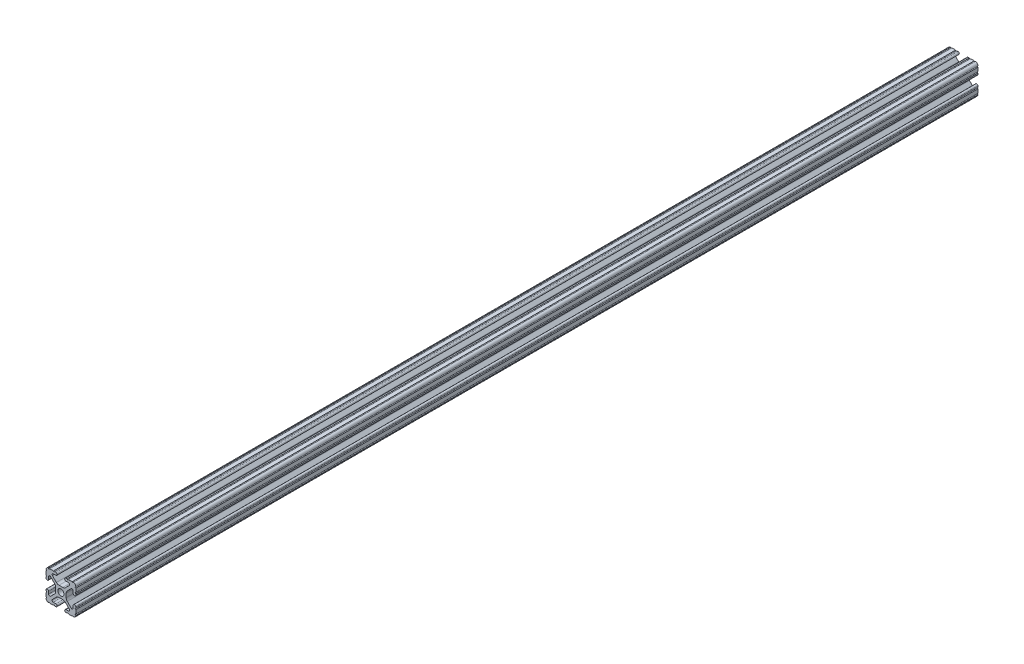
SolidWorks part; units mm, degrees
material "6061-T6 (SS)"
ref_plane "Front Plane" through (0, 0, 0) normal (0, 0, 1) x (1, 0, 0)
ref_plane "Top Plane" through (0, 0, 0) normal (0, 1, 0) x (1, 0, 0)
ref_plane "Right Plane" through (0, 0, 0) normal (1, 0, 0) x (0, 0, -1)
ref_plane "Plane1" through (0, 0, -450.85) normal (0, 0, -1) x (-1, 0, 0)
sketch "Sketch1" plane through (0, 0, -450.85) normal (0, 0, -1) x (-1, 0, 0)
  line L0 (12.7, -9.5504) -> (12.7, -6.3331)
  line L1 (12.7, -5.3171) -> (12.7, -4.3434)
  line L2 (10.4902, -4.3434) -> (10.4902, -6.4748)
  line L3 (8.7558, -7.1932) -> (5.4257, -3.8632)
  line L4 (4.4958, -1.6181) -> (4.4958, 1.6181)
  line L5 (5.4257, 3.8632) -> (8.7558, 7.1932)
  line L6 (10.4902, 6.4748) -> (10.4902, 4.3434)
  line L7 (12.7, 4.3434) -> (12.7, 5.3171)
  line L8 (12.7, 6.3331) -> (12.7, 9.5504)
  line L9 (9.5504, 12.7) -> (6.3331, 12.7)
  line L10 (5.3171, 12.7) -> (4.3434, 12.7)
  line L11 (4.3434, 10.4902) -> (6.4748, 10.4902)
  line L12 (7.1932, 8.7558) -> (3.8632, 5.4257)
  line L13 (1.6181, 4.4958) -> (-1.6181, 4.4958)
  line L14 (-3.8632, 5.4257) -> (-7.1932, 8.7558)
  line L15 (-6.4748, 10.4902) -> (-4.3434, 10.4902)
  line L16 (-4.3434, 12.7) -> (-5.3171, 12.7)
  line L17 (-6.3331, 12.7) -> (-9.5504, 12.7)
  line L18 (-12.7, 9.5504) -> (-12.7, 6.3331)
  line L19 (-12.7, 5.3171) -> (-12.7, 4.3434)
  line L20 (-10.4902, 4.3434) -> (-10.4902, 6.4748)
  line L21 (-8.7558, 7.1932) -> (-5.4257, 3.8632)
  line L22 (-4.4958, 1.6181) -> (-4.4958, -1.6181)
  line L23 (-5.4257, -3.8632) -> (-8.7558, -7.1932)
  line L24 (-10.4902, -6.4748) -> (-10.4902, -4.3434)
  line L25 (-12.7, -4.3434) -> (-12.7, -5.3171)
  line L26 (-12.7, -6.3331) -> (-12.7, -9.5504)
  line L27 (-9.5504, -12.7) -> (-6.3331, -12.7)
  line L28 (-5.3171, -12.7) -> (-4.3434, -12.7)
  line L29 (-4.3434, -10.4902) -> (-6.4748, -10.4902)
  line L30 (-7.1932, -8.7558) -> (-3.8632, -5.4257)
  line L31 (-1.6181, -4.4958) -> (1.6181, -4.4958)
  line L32 (3.8632, -5.4257) -> (7.1932, -8.7558)
  line L33 (6.4748, -10.4902) -> (4.3434, -10.4902)
  line L34 (4.3434, -12.7) -> (5.3171, -12.7)
  line L35 (6.3331, -12.7) -> (9.5504, -12.7)
  arc A0 (12.6998, -10.5664) -> (12.7, -9.5504) centre (12.7, -10.0584) cw
  arc A1 (12.7, -6.3331) -> (12.7, -5.3171) centre (12.7, -5.8251) cw
  arc A2 (12.7, -4.3434) -> (10.4902, -4.3434) centre (11.5951, -4.3434) ccw
  arc A3 (10.4902, -6.4748) -> (8.7558, -7.1932) centre (9.4742, -6.4748) cw
  arc A4 (5.4257, -3.8632) -> (4.4958, -1.6181) centre (7.6708, -1.6181) cw
  arc A5 (4.4958, 1.6181) -> (5.4257, 3.8632) centre (7.6708, 1.6181) cw
  arc A6 (8.7558, 7.1932) -> (10.4902, 6.4748) centre (9.4742, 6.4748) cw
  arc A7 (10.4902, 4.3434) -> (12.7, 4.3434) centre (11.5951, 4.3434) ccw
  arc A8 (12.7, 5.3171) -> (12.7, 6.3331) centre (12.7, 5.8251) cw
  arc A9 (12.7, 9.5504) -> (12.6998, 10.5664) centre (12.7, 10.0584) cw
  arc A10 (12.6998, 10.5664) -> (10.5664, 12.6998) centre (10.5918, 10.5918) ccw
  arc A11 (10.5664, 12.6998) -> (9.5504, 12.7) centre (10.0584, 12.7) cw
  arc A12 (6.3331, 12.7) -> (5.3171, 12.7) centre (5.8251, 12.7) cw
  arc A13 (4.3434, 12.7) -> (4.3434, 10.4902) centre (4.3434, 11.5951) ccw
  arc A14 (6.4748, 10.4902) -> (7.1932, 8.7558) centre (6.4748, 9.4742) cw
  arc A15 (3.8632, 5.4257) -> (1.6181, 4.4958) centre (1.6181, 7.6708) cw
  arc A16 (-1.6181, 4.4958) -> (-3.8632, 5.4257) centre (-1.6181, 7.6708) cw
  arc A17 (-7.1932, 8.7558) -> (-6.4748, 10.4902) centre (-6.4748, 9.4742) cw
  arc A18 (-4.3434, 10.4902) -> (-4.3434, 12.7) centre (-4.3434, 11.5951) ccw
  arc A19 (-5.3171, 12.7) -> (-6.3331, 12.7) centre (-5.8251, 12.7) cw
  arc A20 (-9.5504, 12.7) -> (-10.5664, 12.6998) centre (-10.0584, 12.7) cw
  arc A21 (-10.5664, 12.6998) -> (-12.6998, 10.5664) centre (-10.5918, 10.5918) ccw
  arc A22 (-12.6998, 10.5664) -> (-12.7, 9.5504) centre (-12.7, 10.0584) cw
  arc A23 (-12.7, 6.3331) -> (-12.7, 5.3171) centre (-12.7, 5.8251) cw
  arc A24 (-12.7, 4.3434) -> (-10.4902, 4.3434) centre (-11.5951, 4.3434) ccw
  arc A25 (-10.4902, 6.4748) -> (-8.7558, 7.1932) centre (-9.4742, 6.4748) cw
  arc A26 (-5.4257, 3.8632) -> (-4.4958, 1.6181) centre (-7.6708, 1.6181) cw
  arc A27 (-4.4958, -1.6181) -> (-5.4257, -3.8632) centre (-7.6708, -1.6181) cw
  arc A28 (-8.7558, -7.1932) -> (-10.4902, -6.4748) centre (-9.4742, -6.4748) cw
  arc A29 (-10.4902, -4.3434) -> (-12.7, -4.3434) centre (-11.5951, -4.3434) ccw
  arc A30 (-12.7, -5.3171) -> (-12.7, -6.3331) centre (-12.7, -5.8251) cw
  arc A31 (-12.7, -9.5504) -> (-12.6998, -10.5664) centre (-12.7, -10.0584) cw
  arc A32 (-12.6998, -10.5664) -> (-10.5664, -12.6998) centre (-10.5918, -10.5918) ccw
  arc A33 (-10.5664, -12.6998) -> (-9.5504, -12.7) centre (-10.0584, -12.7) cw
  arc A34 (-6.3331, -12.7) -> (-5.3171, -12.7) centre (-5.8251, -12.7) cw
  arc A35 (-4.3434, -12.7) -> (-4.3434, -10.4902) centre (-4.3434, -11.5951) ccw
  arc A36 (-6.4748, -10.4902) -> (-7.1932, -8.7558) centre (-6.4748, -9.4742) cw
  arc A37 (-3.8632, -5.4257) -> (-1.6181, -4.4958) centre (-1.6181, -7.6708) cw
  arc A38 (1.6181, -4.4958) -> (3.8632, -5.4257) centre (1.6181, -7.6708) cw
  arc A39 (7.1932, -8.7558) -> (6.4748, -10.4902) centre (6.4748, -9.4742) cw
  arc A40 (4.3434, -10.4902) -> (4.3434, -12.7) centre (4.3434, -11.5951) ccw
  arc A41 (5.3171, -12.7) -> (6.3331, -12.7) centre (5.8251, -12.7) cw
  arc A42 (9.5504, -12.7) -> (10.5664, -12.6998) centre (10.0584, -12.7) cw
  arc A43 (10.5664, -12.6998) -> (12.6998, -10.5664) centre (10.5918, -10.5918) ccw
  circle A44 centre (0, 0) radius 2.6035
extrude "Boss-Extrude1" add sketch "Sketch1" against normal blind 768.35
